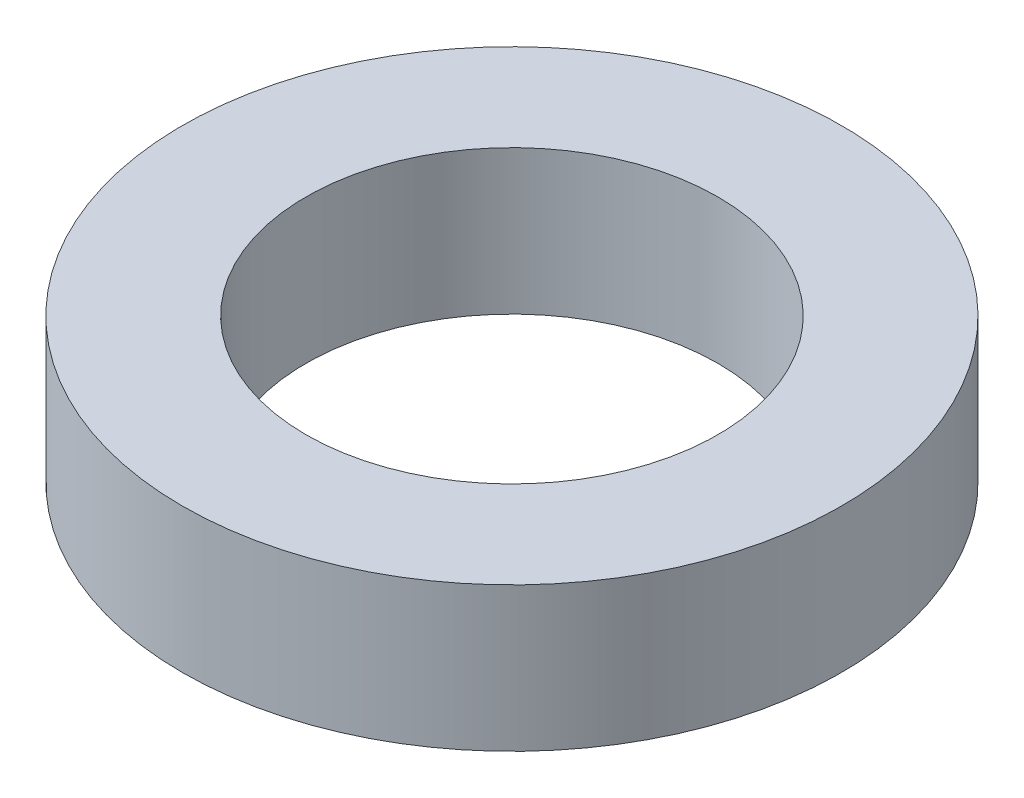
SolidWorks part; units mm, degrees
ref_plane "Front Plane" through (0, 0, 0) normal (0, 0, 1) x (1, 0, 0)
ref_plane "Top Plane" through (0, 0, 0) normal (0, 1, 0) x (1, 0, 0)
ref_plane "Right Plane" through (0, 0, 0) normal (1, 0, 0) x (0, 0, -1)
sketch "Sketch1" plane through (0, 0, 0) normal (0, 1, 0) x (1, 0, 0)
  circle A0 centre (0, 0) radius 10
  circle A1 centre (0, 0) radius 16
  dimension "D1" = 20
  dimension "D2" = 32
extrude "Boss-Extrude1" add sketch "Sketch1" along normal blind 7
